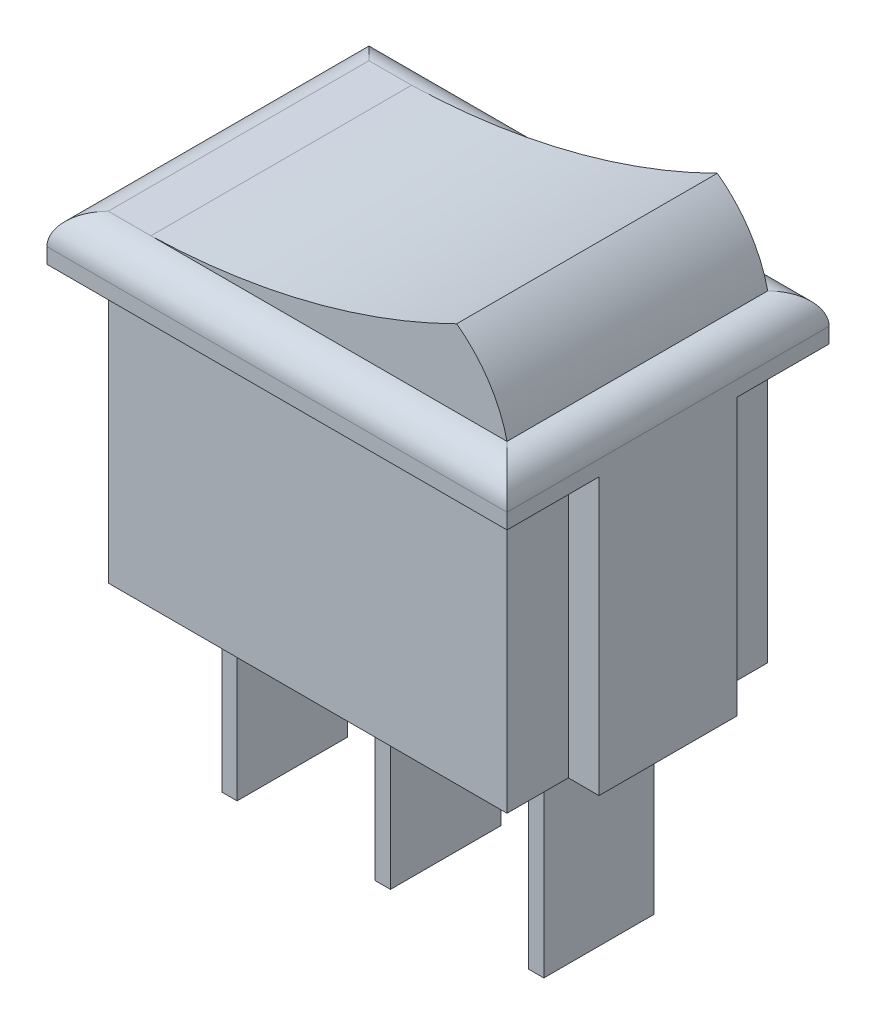
SolidWorks part; units mm, degrees
ref_plane "Plan de face" through (0, 0, 0) normal (0, 0, 1) x (1, 0, 0)
ref_plane "Plan de dessus" through (0, 0, 0) normal (0, 1, 0) x (1, 0, 0)
ref_plane "Plan de droite" through (0, 0, 0) normal (1, 0, 0) x (0, 0, -1)
sketch "Esquisse1" plane through (0, 0, 0) normal (0, 1, 0) x (1, 0, 0)
  line L0 (6.5, 8.5) -> (6.5, 0) construction
  line L1 (0, 0) -> (13, 0)
  line L2 (0, 0) -> (0, 8.5)
  line L3 (0, 8.5) -> (13, 8.5)
  line L4 (13, 0) -> (13, 8.5)
  line L5 (-1, 6.5) -> (0, 6.5)
  line L6 (-1, 6.5) -> (-1, 2)
  line L7 (-1, 2) -> (0, 2)
  line L8 (0, 6.5) -> (0, 2)
  line L9 (13, 6.5) -> (13, 2)
  line L10 (14, 2) -> (13, 2)
  line L11 (14, 6.5) -> (14, 2)
  line L12 (14, 6.5) -> (13, 6.5)
  point P9 (0, 4.25)
  point P10 (0, 4.25)
  dimension "D1" = 13
  dimension "D2" = 1
  dimension "8.5" = 8.5
  dimension "D3" = 4.5
extrude "Boss.-Extru.1" add sketch "Esquisse1" along normal blind 9 contours L3 L0 L1 L4 | L0 L3 L2 L1 | L6 L7 L2 L5 | L11 L10 L9 L12
sketch "Esquisse2" plane through (0, 9, 0) normal (0, 1, 0) x (1, 0, 0)
  line L0 (0, 8.5) -> (13, 0) construction
  line L1 (-1, 9.5) -> (14, -1) construction
  line L2 (-1, 9.5) -> (14, 9.5)
  line L3 (-1, 9.5) -> (-1, -1)
  line L4 (-1, -1) -> (14, -1)
  line L5 (14, 9.5) -> (14, -1)
  point P8 (6.5, 4.25)
  point P9 (6.5, 4.25)
  dimension "D1" = 15
  dimension "D2" = 10.5
extrude "Boss.-Extru.2" add sketch "Esquisse2" along normal blind 1.5
fillet "Congé1" radius 1 4 edges at (6.5, 10.5, -9.5) (6.5, 10.5, 1) (14, 10.5, -4.25) (-1, 10.5, -4.25)
sketch "Esquisse3" plane through (0, 0, 0) normal (0, -1, 0) x (1, 0, 0)
  line L0 (6.25, -2.45) -> (6.75, -2.45)
  line L1 (1.25, -2.45) -> (1.75, -2.45)
  line L2 (1.25, -2.45) -> (1.25, -6.05)
  line L3 (1.25, -6.05) -> (1.75, -6.05)
  line L4 (1.75, -2.45) -> (1.75, -6.05)
  line L5 (6.25, -2.45) -> (6.25, -6.05)
  line L6 (6.25, -6.05) -> (6.75, -6.05)
  line L7 (6.75, -2.45) -> (6.75, -6.05)
  line L8 (11.25, -2.45) -> (11.75, -2.45)
  line L9 (11.25, -2.45) -> (11.25, -6.05)
  line L10 (11.25, -6.05) -> (11.75, -6.05)
  line L11 (11.75, -2.45) -> (11.75, -6.05)
  line L12 (6.25, -2.45) -> (6.75, -6.05) construction
  line L13 (0, 0) -> (13, -8.5) construction
  point P4 (6.5, -4.25)
  point P17 (6.5, -4.25)
  dimension "D1" = 0.5
  dimension "D2" = 3.6
  dimension "D4" = 4.5
  dimension "D3" = 3
extrude "Boss.-Extru.3" add sketch "Esquisse3" along normal blind 6.5
sketch "Esquisse4" plane through (0, 0, -8.5) normal (0, 0, -1) x (-1, 0, 0)
  line L0 (-13, 10.5) -> (0, 10.5)
  line L1 (-13, 10.5) -> (-13, 13)
  line L2 (-13, 13) -> (-11.3582, 13) construction
  line L3 (-13, 9) -> (-13, 0) construction
  line L4 (-13, 10.5) -> (0, 10.5)
  arc A1 (-4.7435, 10.8353) -> (-4.6526, 10.5) centre (-8.8263, 9.5481) ccw
  circle A2 centre (-0.6941, 34.3981) radius 23.9082
  dimension "D2" = 8.5618
  dimension "D3" = 47.8163
  dimension "D1" = 2.5
  dimension "D4" = 4.1737
extrude "Boss.-Extru.4" add sketch "Esquisse4" against normal up to surface (8.5 mm away) contours A2 A1 L0 L4
